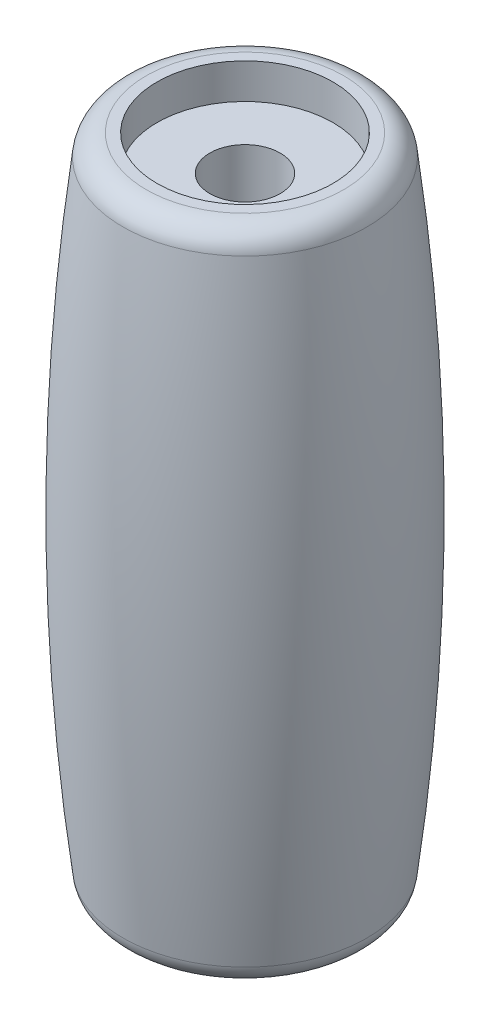
SolidWorks part; units mm, degrees
ref_plane "Front Plane" through (0, 0, 0) normal (0, 0, 1) x (1, 0, 0)
ref_plane "Top Plane" through (0, 0, 0) normal (0, 1, 0) x (1, 0, 0)
ref_plane "Right Plane" through (0, 0, 0) normal (1, 0, 0) x (0, 0, -1)
sketch "Sketch1" plane through (0, 0, 0) normal (0, 0, 1) x (1, 0, 0)
  line L0 (0, 0) -> (-4.2093, 0)
  line L1 (0, 28) -> (-4.2093, 28)
  line L2 (0, 0) -> (0, 28)
  arc A1 (-5.2019, 27.1212) -> (-5.2019, 0.8788) centre (102.2566, 14) ccw
  arc A2 (-4.2093, 0) -> (-5.2019, 0.8788) centre (-4.2093, 1) cw
  arc A3 (-4.2093, 28) -> (-5.2019, 27.1212) centre (-4.2093, 27) ccw
  point P8 (-6, 14)
  point P12 (-2.1046, 28)
  point P16 (-5.0909, 0)
  point P19 (-5.0909, 28)
  dimension "D1" = 6
  dimension "D2" = 28
  dimension "D3" = 1
revolve "Revolve1" add sketch "Sketch1" angle 360 about L2
sketch "Sketch2" plane through (0, 28, 0) normal (0, 1, 0) x (1, 0, 0)
  circle A0 centre (0, 0) radius 3.75
  dimension "D1" = 7.5
extrude "Cut-Extrude1" cut sketch "Sketch2" against normal blind 1.5
sketch "Sketch3" plane through (0, 0, 0) normal (0, -1, 0) x (1, 0, 0)
  circle A0 centre (0, 0) radius 3.75
  dimension "D1" = 7.5
extrude "Cut-Extrude2" cut sketch "Sketch3" against normal blind 1.5
sketch "Sketch4" plane through (0, 1.5, 0) normal (0, -1, 0) x (-1, 0, 0)
  circle A0 centre (0, 0) radius 1.5
  dimension "D1" = 3
extrude "Cut-Extrude3" cut sketch "Sketch4" against normal through all
